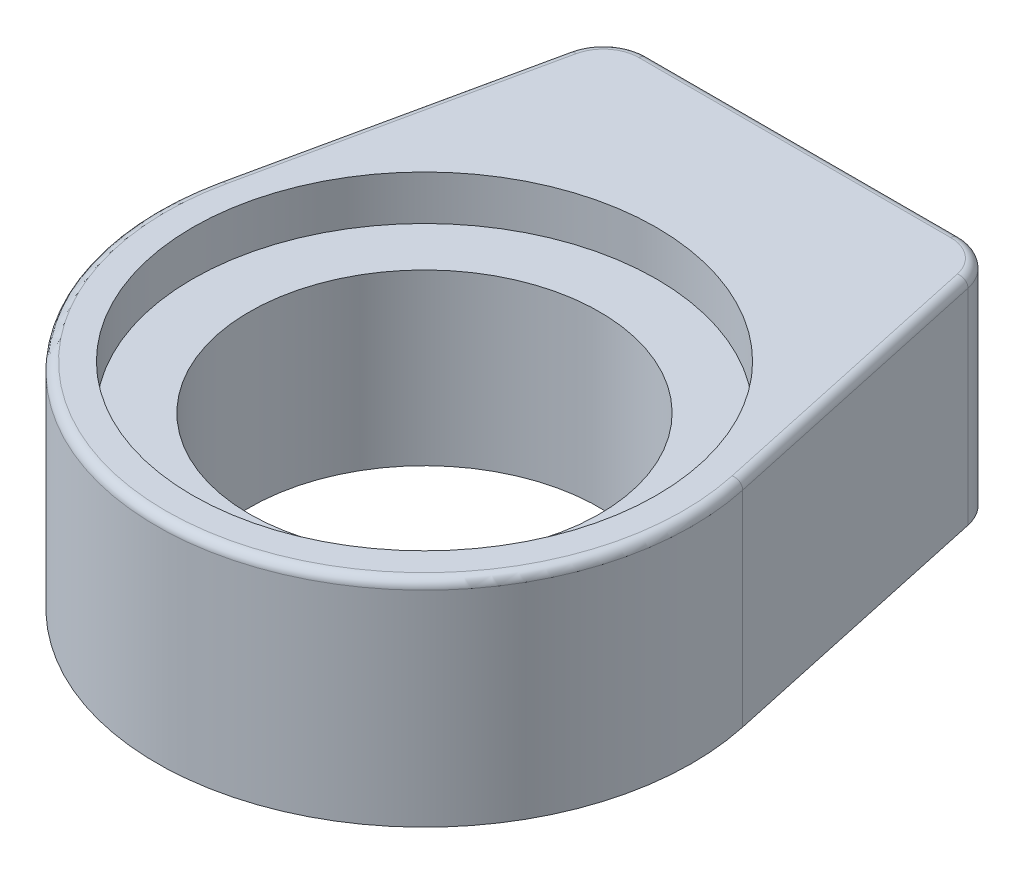
SolidWorks part; units mm, degrees
material "Delrin 2700 NC010, Low Viscosity Acetal Copolymer (SS)"
ref_plane "Front Plane" through (0, 0, 0) normal (0, 0, 1) x (1, 0, 0)
ref_plane "Top Plane" through (0, 0, 0) normal (0, 1, 0) x (1, 0, 0)
ref_plane "Right Plane" through (0, 0, 0) normal (1, 0, 0) x (0, 0, -1)
sketch "Sketch5" plane through (0, 0, 0) normal (0, 1, 0) x (1, 0, 0)
  line L0 (-10.922, 21.59) -> (10.922, 21.59)
  line L1 (0, 0) -> (0, 37.164) construction
  line L2 (-14.8954, 3.2223) -> (-10.922, 21.59)
  line L3 (14.8954, 3.2223) -> (10.922, 21.59)
  arc A0 (-14.8954, 3.2223) -> (14.8954, 3.2223) centre (0, 0) ccw
  dimension "D1" = 30.48
  dimension "D2" = 21.59
  dimension "D3" = 21.844
extrude "Extrude1" add sketch "Sketch5" along normal blind 12.192
fillet "Fillet2" radius 2.54 2 edges at (-10.922, 6.096, -21.59) (10.922, 6.096, -21.59)
fillet "Fillet1" radius 0.508 6 edges at (0, 12.192, -21.59) (13.1254, 12.192, -11.4047) (0, 12.192, 15.24) (-13.1254, 12.192, -11.4047) (10.4676, 12.192, -21.0268) (-10.4676, 12.192, -21.0268)
sketch "Sketch6" plane through (0, 12.192, 0) normal (0, 1, 0) x (1, 0, 0)
  circle A0 centre (0, 0) radius 9.9695
  dimension "D1" = 19.939
extrude "Extrude2" cut sketch "Sketch6" against normal through all
sketch "Sketch7" plane through (0, 12.192, 0) normal (0, 1, 0) x (1, 0, 0)
  circle A0 centre (0, 0) radius 13.208
  dimension "D1" = 26.416
extrude "Extrude3" cut sketch "Sketch7" against normal blind 2.54
